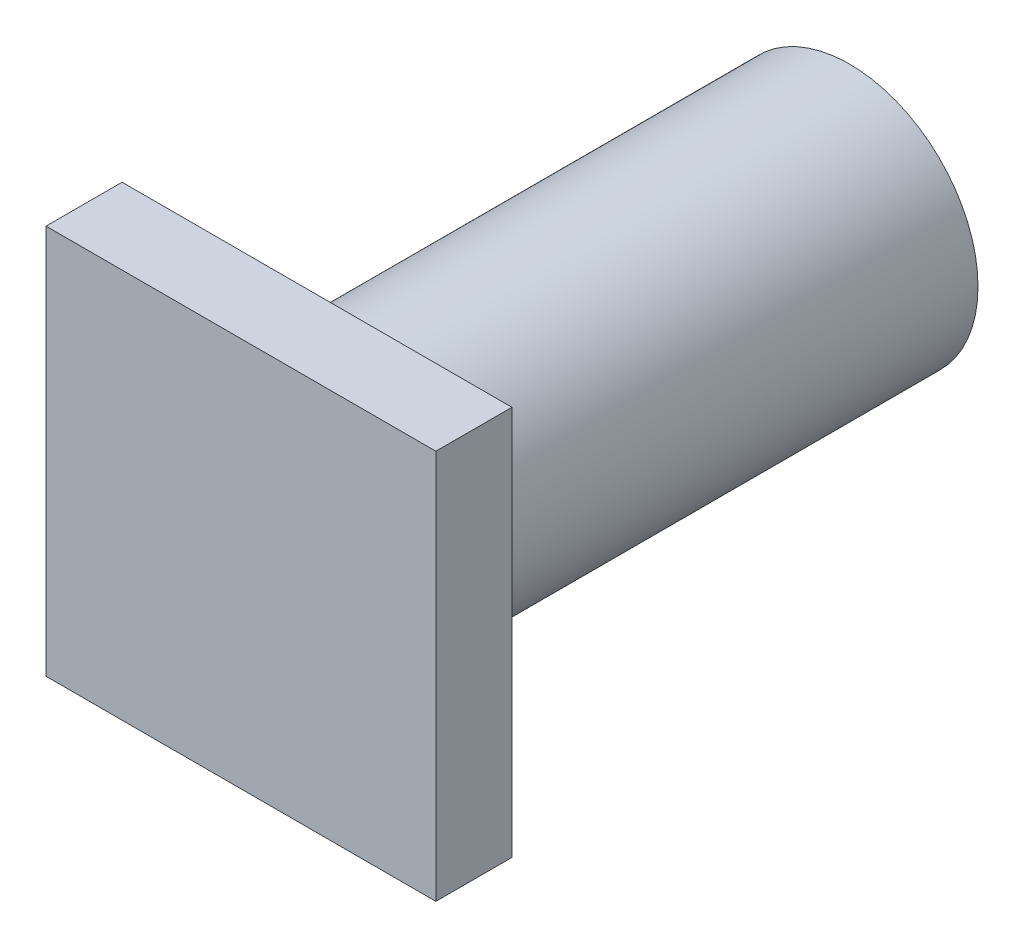
SolidWorks part; units mm, degrees
ref_plane "Front Plane" through (0, 0, 0) normal (0, 0, 1) x (1, 0, 0)
ref_plane "Top Plane" through (0, 0, 0) normal (0, 1, 0) x (1, 0, 0)
ref_plane "Right Plane" through (0, 0, 0) normal (1, 0, 0) x (0, 0, -1)
sketch "Sketch1" plane through (0, 0, 0) normal (0, 0, 1) x (1, 0, 0)
  circle A0 centre (-8.1233, -5.9278) radius 16.8924
extrude "Boss-Extrude1" add sketch "Sketch1" along normal blind 70
sketch "Sketch2" plane through (0, 0, 70) normal (0, 0, 1) x (1, 0, 0)
  line L1 (-33.7479, -31.5524) -> (17.5012, -31.5524)
  line L2 (-33.7479, -31.5524) -> (-33.7479, 19.6967)
  line L3 (-33.7479, 19.6967) -> (17.5012, 19.6967)
  line L4 (17.5012, -31.5524) -> (17.5012, 19.6967)
  line L5 (-33.7479, -31.5524) -> (17.5012, 19.6967) construction
  line L6 (-33.7479, 19.6967) -> (17.5012, -31.5524) construction
  circle A0 centre (-8.1233, -5.9278) radius 16.8924 construction
  point P0 (-8.1233, -5.9278)
extrude "Boss-Extrude2" add sketch "Sketch2" along normal blind 10
